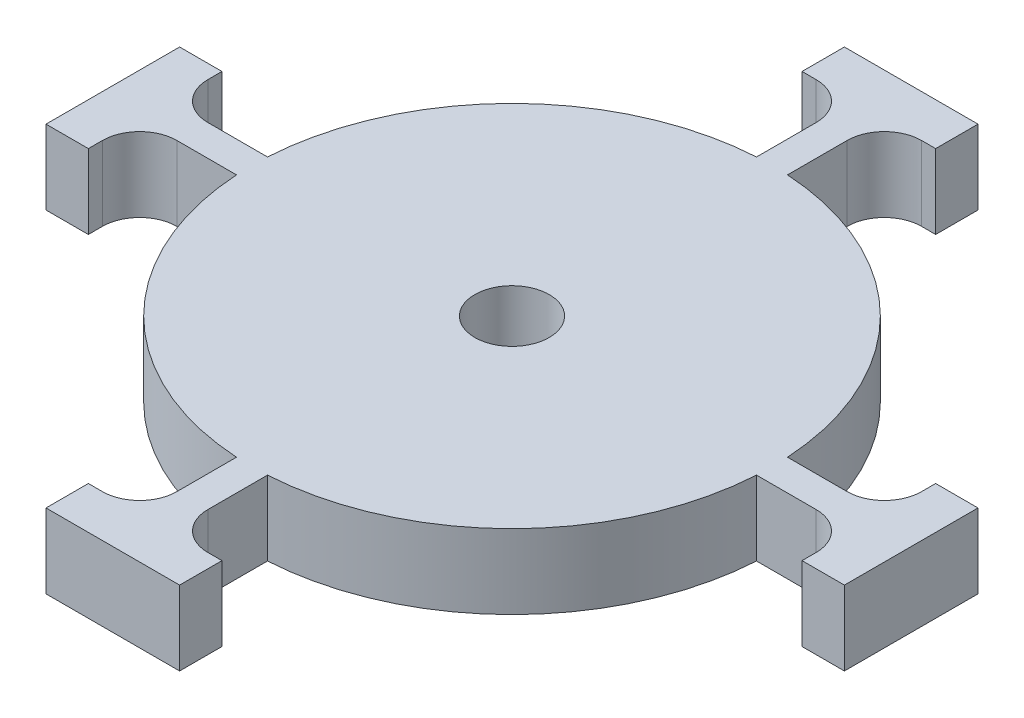
SolidWorks part; units mm, degrees
ref_plane "Front Plane" through (0, 0, 0) normal (0, 0, 1) x (1, 0, 0)
ref_plane "Top Plane" through (0, 0, 0) normal (0, 1, 0) x (1, 0, 0)
ref_plane "Right Plane" through (0, 0, 0) normal (1, 0, 0) x (0, 0, -1)
sketch "Sketch1" plane through (0, 0, 0) normal (0, 1, 0) x (1, 0, 0)
  line L0 (0, 138.1266) -> (0, -138.1266) construction
  line L1 (199.8798, 0) -> (-199.8798, 0) construction
  line L2 (101.7717, -101.7717) -> (-101.7717, 101.7717) construction
  line L3 (-123.6471, -123.6471) -> (123.6471, 123.6471) construction
  line L4 (-2.0839, 34.9379) -> (-2.0839, 47.9502)
  line L5 (-2.0839, 47.9502) -> (-8.9766, 47.9502)
  line L6 (-8.9766, 47.9502) -> (-8.9766, 53.6427)
  line L7 (-8.9766, 53.6427) -> (8.9766, 53.6427)
  line L8 (2.0839, 34.9379) -> (2.0839, 47.9502)
  line L9 (8.9766, 47.9502) -> (8.9766, 53.6427)
  line L10 (2.0839, 47.9502) -> (8.9766, 47.9502)
  line L11 (-2.0839, -34.9379) -> (-2.0839, -47.9502)
  line L12 (2.0839, -34.9379) -> (2.0839, -47.9502)
  line L13 (2.0839, -47.9502) -> (8.9766, -47.9502)
  line L14 (8.9766, -47.9502) -> (8.9766, -53.6427)
  line L15 (-8.9766, -53.6427) -> (8.9766, -53.6427)
  line L16 (-8.9766, -47.9502) -> (-8.9766, -53.6427)
  line L17 (-2.0839, -47.9502) -> (-8.9766, -47.9502)
  line L18 (-34.9379, 2.0839) -> (-47.9502, 2.0839)
  line L19 (-34.9379, -2.0839) -> (-47.9502, -2.0839)
  line L20 (-47.9502, -2.0839) -> (-47.9502, -8.9766)
  line L21 (-47.9502, -8.9766) -> (-53.6427, -8.9766)
  line L22 (-53.6427, 8.9766) -> (-53.6427, -8.9766)
  line L23 (-47.9502, 8.9766) -> (-53.6427, 8.9766)
  line L24 (-47.9502, 2.0839) -> (-47.9502, 8.9766)
  line L25 (34.9379, -2.0839) -> (47.9502, -2.0839)
  line L26 (34.9379, 2.0839) -> (47.9502, 2.0839)
  line L27 (47.9502, 2.0839) -> (47.9502, 8.9766)
  line L28 (47.9502, 8.9766) -> (53.6427, 8.9766)
  line L29 (53.6427, -8.9766) -> (53.6427, 8.9766)
  line L30 (47.9502, -8.9766) -> (53.6427, -8.9766)
  line L31 (47.9502, -2.0839) -> (47.9502, -8.9766)
  circle A0 centre (0, 0) radius 35
  circle A1 centre (0, 0) radius 5
  point P6 (0, 0)
  point P9 (0, 0)
  point P12 (0, 0)
  point P15 (0, 0)
  point P23 (0, 53.6427)
  point P32 (0, -53.6427)
  point P41 (-53.6427, 0)
  point P50 (53.6427, 0)
extrude "Boss-Extrude1" add sketch "Sketch1" along normal blind 10 contours A0 | A0 L25 L31 L30 L29 L28 L27 L26 | A0 L11 L17 L16 L15 L14 L13 L12 | A0 L18 L24 L23 L22 L21 L20 L19 | A0 L8 L10 L9 L7 L6 L5 L4
fillet "Fillet1" radius 5 8 edges at (2.0839, 5, -47.9502) (-47.9502, 5, -2.0839) (-47.9502, 5, 2.0839) (-2.0839, 5, 47.9502) (2.0839, 5, 47.9502) (47.9502, 5, 2.0839) (47.9502, 5, -2.0839) (-2.0839, 5, -47.9502)
